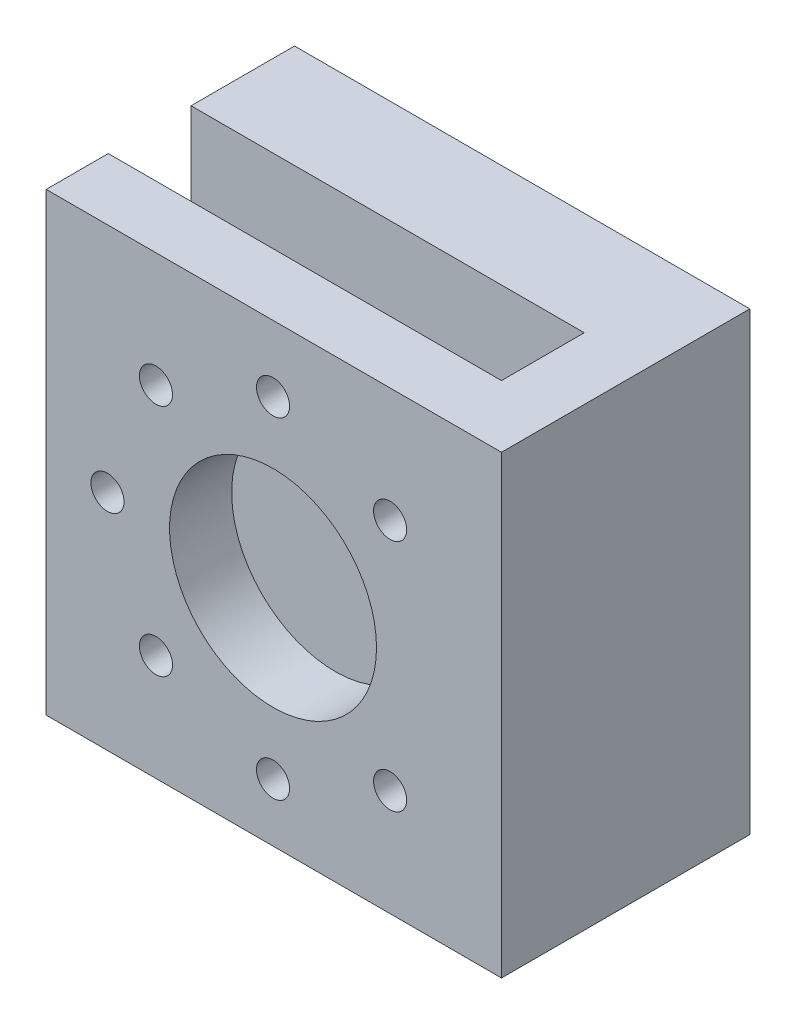
SolidWorks part; units mm, degrees
material "AISI 1020"
ref_plane "Plano frontal" through (0, 0, 0) normal (0, 0, 1) x (1, 0, 0)
ref_plane "Plano superior" through (0, 0, 0) normal (0, 1, 0) x (1, 0, 0)
ref_plane "Plano direito" through (0, 0, 0) normal (1, 0, 0) x (0, 0, -1)
sketch "Esboço1" plane through (0, 0, 0) normal (0, 0, 1) x (1, 0, 0)
  line L7 (6.8202, 18.7273) -> (6.8202, 22.387)
  line L8 (6.8202, 22.387) -> (6.1802, 22.387)
  line L9 (-6.4404, 18.7273) -> (-6.4404, 22.387)
  line L10 (-6.4404, 22.387) -> (6.1802, 22.387)
  line L11 (-54.8101, 55.9758) -> (55.1899, 55.9758)
  line L12 (-54.8101, 55.9758) -> (-54.8101, -54.0242)
  line L13 (55.1899, 55.9758) -> (55.1899, -54.0242)
  line L14 (-54.8101, -54.0242) -> (-1.3101, -54.0242)
  line L18 (1.6899, -18.019) -> (1.6899, -54.0242)
  line L19 (-1.3101, 55.9758) -> (1.6899, 55.9758)
  line L24 (1.6899, -54.0242) -> (55.1899, -54.0242)
  line L25 (-1.3101, -18.019) -> (-1.3101, -54.0242)
  line L31 (-28.0943, -27.3626) -> (28.4742, 29.206) construction
  line L32 (-28.0943, 29.206) -> (28.4742, -27.3626) construction
  arc A4 (-6.4404, 18.7273) -> (-1.3101, -18.019) centre (0.1899, 0.9217) ccw
  arc A5 (1.6899, -18.019) -> (6.8202, 18.7273) centre (0.1899, 0.9217) ccw
  dimension "D4" = 90
  dimension "D2" = 110
  dimension "D3" = 110
extrude "Ressalto-extrusão2" add sketch "Esboço1" along normal blind 25
sketch "Esboço5" plane through (-54.8101, 0, 0) normal (-1, 0, 0) x (0, 0, 1)
  line L0 (0, 55.9758) -> (0, -54.0242) construction
  line L1 (25, -54.0242) -> (0, -54.0242) construction
  circle A0 centre (12.5, -41.0242) radius 4
  dimension "D1" = 12.5
  dimension "D2" = 13
  dimension "D3" = 8
extrude "Corte-extrusão3" cut sketch "Esboço5" against normal blind 85
cosmetic thread "Representação de rosca1" parameters "D2"=10
sketch "Esboço6" plane through (-54.8101, 0, 0) normal (-1, 0, 0) x (0, 0, 1)
  circle A0 centre (12.5, -41.0242) radius 7
extrude "Corte-extrusão4" cut sketch "Esboço6" against normal blind 20
thread "Rosca1" pitch 1.25 start angle 0, offset 0, length 32, pitch 1.25, diameter 8
ref_plane "Plano1" through (-34.8101, -41.0242, 8.5) normal (0, -1, 0) x (0, 0, -1)
sketch "Perfil da rosca1" plane through (-34.8101, -41.0242, 8.5) normal (0, -1, 0) x (0, 0, -1)
  line L0 (0, 0) -> (0, 1.25) construction
  line L11 (0, 0) -> (0, 1.0937)
  line L12 (0, 1.0937) -> (-0.6766, 0.7031)
  line L13 (-0.6766, 0.7031) -> (-0.6766, 0.3906)
  line L15 (-0.6766, 0.3906) -> (0, 0)
  line L17 (-0.6766, 0.5469) -> (0, 0.5469) construction
  point P2 (0, 0)
  dimension "Pitch" = 1.25
  dimension "Profile_Angle" = 60
  dimension "Profile_Land" = 0.3125
  dimension "Profile_Height" = 0.6766
thread "Rosca2" pitch 1.25 start angle 0, offset 0, length 20, pitch 1.25, diameter 8
ref_plane "Plano2" through (1.6899, -41.0242, 8.5) normal (0, -1, 0) x (0, 0, -1)
sketch "Perfil da rosca2" plane through (1.6899, -41.0242, 8.5) normal (0, -1, 0) x (0, 0, -1)
  line L0 (0, 0) -> (0, 1.25) construction
  line L11 (0, 0) -> (0, 1.0937)
  line L12 (0, 1.0937) -> (-0.6766, 0.7031)
  line L13 (-0.6766, 0.7031) -> (-0.6766, 0.3906)
  line L15 (-0.6766, 0.3906) -> (0, 0)
  line L17 (-0.6766, 0.5469) -> (0, 0.5469) construction
  point P2 (0, 0)
  dimension "Pitch" = 1.25
  dimension "Profile_Angle" = 60
  dimension "Profile_Land" = 0.3125
  dimension "Profile_Height" = 0.6766
sketch "Esboço12" plane through (0, 0, 25) normal (0, 0, 1) x (1, 0, 0)
  line L0 (1.6899, -54.0242) -> (55.1899, -54.0242) construction
  line L1 (55.1899, 55.9758) -> (40.1899, 55.9758)
  line L2 (55.1899, 55.9758) -> (55.1899, -54.0242)
  line L3 (55.1899, -54.0242) -> (40.1899, -54.0242)
  line L4 (40.1899, 55.9758) -> (40.1899, -54.0242)
  dimension "D1" = 15
extrude "Ressalto-extrusão3" add sketch "Esboço12" along normal blind 20
sketch "Esboço13" plane through (0, 0, 45) normal (0, 0, 1) x (1, 0, 0)
  line L1 (55.1899, 55.9758) -> (-54.8101, 55.9758)
  line L2 (55.1899, 55.9758) -> (55.1899, -54.0242)
  line L3 (55.1899, -54.0242) -> (-54.8101, -54.0242)
  line L4 (-54.8101, 55.9758) -> (-54.8101, -54.0242)
  dimension "D1" = 110
  dimension "D2" = 110
extrude "Ressalto-extrusão4" add sketch "Esboço13" along normal blind 15
sketch "Esboço14" plane through (0, 0, 60) normal (0, 0, 1) x (1, 0, 0)
  line L6 (28.2843, -28.2843) -> (-28.2843, 28.2843) construction
  line L7 (28.2843, 28.2843) -> (-28.2843, -28.2843) construction
  circle A1 centre (0, 0) radius 25
  circle A3 centre (0, 40) radius 4
  circle A4 centre (-40, 0) radius 4
  circle A6 centre (0, -40) radius 4
  circle A7 centre (-28.2843, 28.2843) radius 4
  circle A8 centre (28.2843, 28.2843) radius 4
  circle A9 centre (28.2843, -28.2843) radius 4
  circle A10 centre (-28.2843, -28.2843) radius 4
extrude "Corte-extrusão5" cut sketch "Esboço14" against normal blind 15
cosmetic thread "Representação de rosca2" parameters "D2"=10
cosmetic thread "Representação de rosca3" parameters "D2"=10
cosmetic thread "Representação de rosca4" parameters "D2"=10
cosmetic thread "Representação de rosca5" parameters "D2"=10
cosmetic thread "Representação de rosca6" parameters "D2"=10
cosmetic thread "Representação de rosca7" parameters "D2"=10
cosmetic thread "Representação de rosca8" parameters "D2"=10
cosmetic thread "Representação de rosca9" parameters "D2"=10
cosmetic thread "Representação de rosca10" parameters "D2"=10
cosmetic thread "Representação de rosca11" parameters "D2"=10
cosmetic thread "Representação de rosca12" parameters "D2"=10
cosmetic thread "Representação de rosca13" parameters "D2"=10
cosmetic thread "Representação de rosca14" parameters "D2"=10
cosmetic thread "Representação de rosca15" parameters "D2"=10
